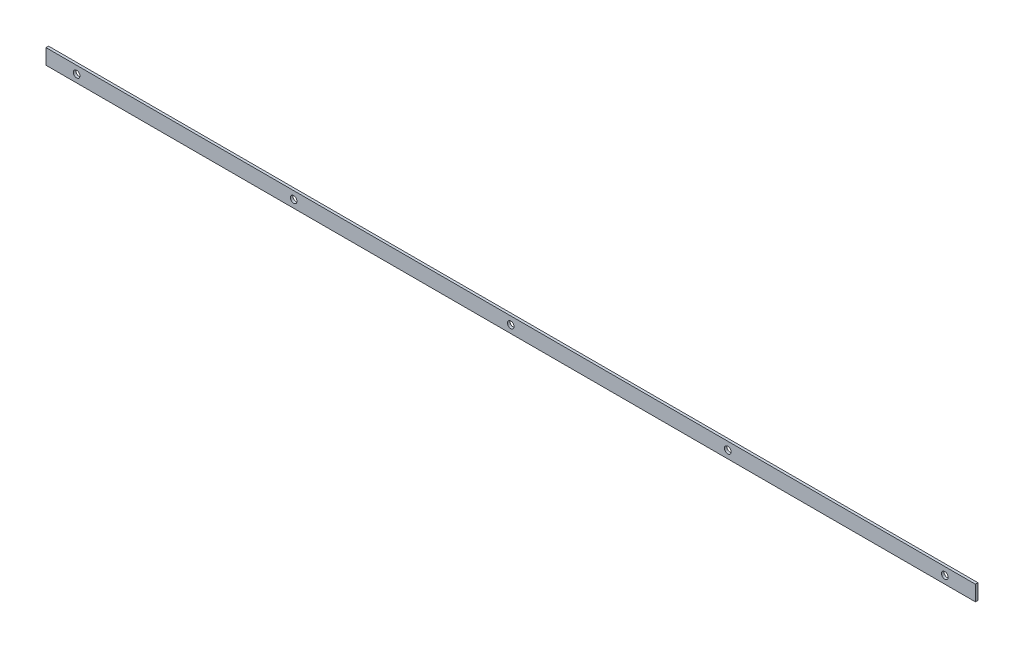
SolidWorks part; units mm, degrees
ref_plane "Plan de face" through (0, 0, 0) normal (0, 0, 1) x (1, 0, 0)
ref_plane "Plan de dessus" through (0, 0, 0) normal (0, 1, 0) x (1, 0, 0)
ref_plane "Plan de droite" through (0, 0, 0) normal (1, 0, 0) x (0, 0, -1)
sketch "Esquisse1" plane through (0, 0, 0) normal (0, 0, 1) x (1, 0, 0)
  line L0 (-910, 0) -> (910, 0)
other "Elément mécano-soudé1"
ref_plane "Plan1" through (-910, 0, 0) normal (1, 0, 0) x (0, 1, 0)
sketch "plat" plane through (-910, 0, 0) normal (1, 0, 0) x (0, 1, 0)
  line L0 (-15, 0) -> (15, 0) construction
  line L1 (-15, 2.5) -> (15, 2.5)
  line L2 (-15, 2.5) -> (-15, -2.5)
  line L3 (-15, -2.5) -> (15, -2.5)
  line L4 (15, 2.5) -> (15, -2.5)
  line L5 (0, 2.5) -> (0, -2.5) construction
  point P8 (0, 0)
  dimension "B" = 30
  dimension "A" = 5
sketch "Esquisse2" plane through (0, 0, -2.5) normal (0, 0, -1) x (-1, 0, 0)
  line L0 (910, 0) -> (-910, 0) construction
  line L1 (910, -15) -> (910, 15) construction
  line L2 (-910, -15) -> (-910, 15) construction
  point P0 (850, 0)
  point P5 (-850, 0)
ref_plane "Plan2" through (850, 0, 0) normal (1, 0, 0) x (0, 0, -1)
hole_wizard "Diamètre du perçage Ø13.0 (13)1" positions "Esquisse3" profile "Esquisse4" hole size "Ø13.0" standard "ISO" end condition through all
sketch "Esquisse3" plane through (0, 0, -2.5) normal (0, 0, -1) x (-1, 0, 0)
  point P0 (850, 0)
sketch "Esquisse4" plane through (-850, 0, -2.5) normal (1, 0, 0) x (0, 1, 0)
  line L0 (0, 0) -> (0, 5)
  line L1 (0, 5) -> (6.5, 5)
  line L2 (6.5, 5) -> (6.5, 0)
  line L5 (6.5, 0) -> (0, 0)
  line L11 (0, -6.35) -> (0, 107.95) construction
  dimension "Diamètre du perçage jusqu'au prochain" = 13
  dimension "Profondeur du perçage jusqu'au prochain" = 5
pattern_linear "Répétition linéaire2" count 5 spacing 425 along (1, 0, 0) of "Diamètre du perçage Ø13.0 (13)1"
equation "\"D2@Esquisse2\"=\"D1@Esquisse2\""
